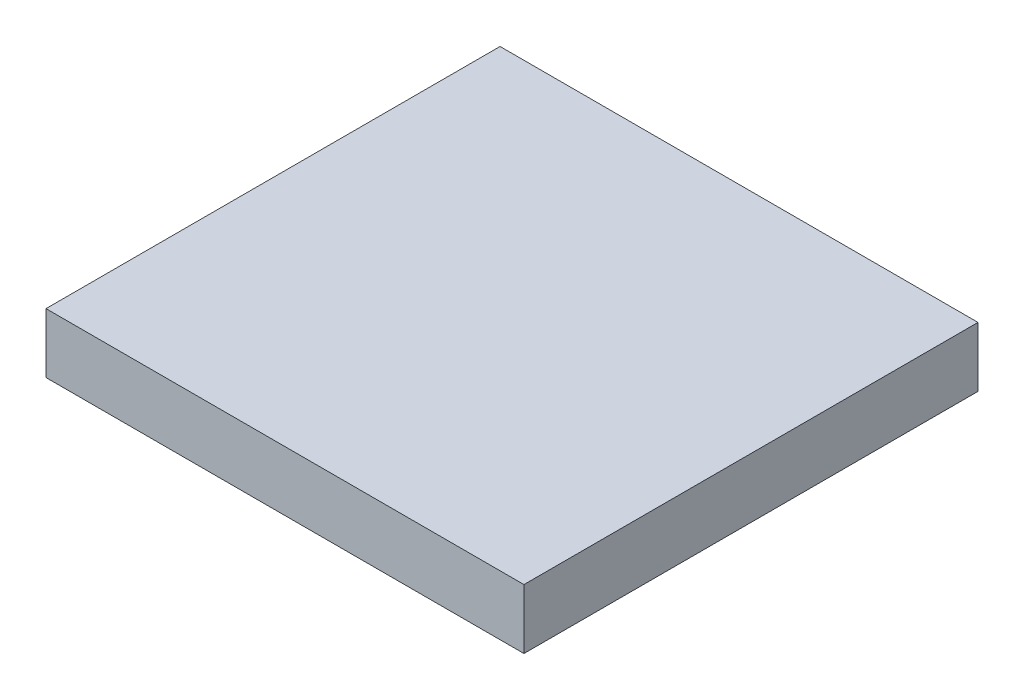
SolidWorks part; units mm, degrees
ref_plane "Front Plane" through (0, 0, 0) normal (0, 0, 1) x (1, 0, 0)
ref_plane "Top Plane" through (0, 0, 0) normal (0, 1, 0) x (1, 0, 0)
ref_plane "Right Plane" through (0, 0, 0) normal (1, 0, 0) x (0, 0, -1)
sketch "Sketch1" plane through (0, 0, 0) normal (0, 1, 0) x (1, 0, 0)
  line L0 (-6.35, 5.715) -> (6.35, 5.715)
  line L1 (6.35, 5.715) -> (6.35, -6.35)
  line L2 (6.35, -6.35) -> (-6.35, -6.35)
  line L3 (0, -6.35) -> (0, 5.715) construction
  line L4 (-6.35, 5.715) -> (-6.35, -6.35)
  dimension "D1" = 12.7
  dimension "D2" = 12.065
extrude "LowerBase" add sketch "Sketch1" along normal blind 1.5875
